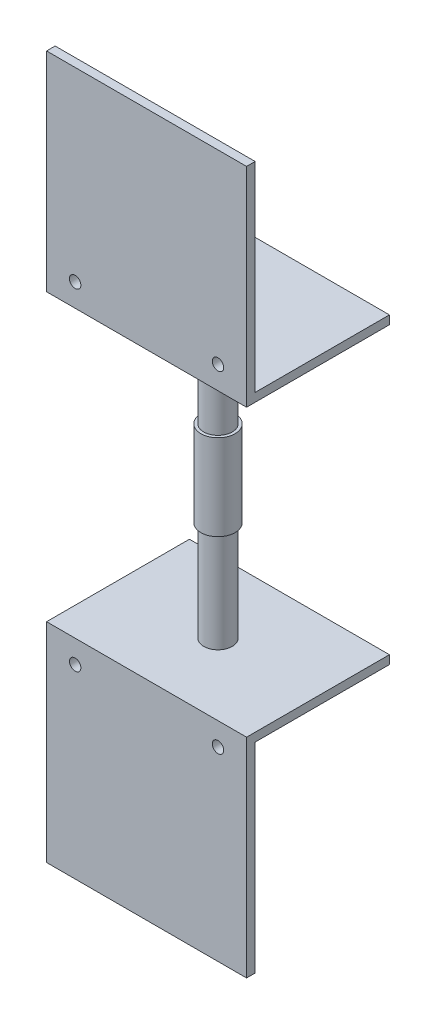
SolidWorks part; units mm, degrees
ref_plane "Front Plane" through (0, 0, 0) normal (0, 0, 1) x (1, 0, 0)
ref_plane "Top Plane" through (0, 0, 0) normal (0, 1, 0) x (1, 0, 0)
ref_plane "Right Plane" through (0, 0, 0) normal (1, 0, 0) x (0, 0, -1)
sketch "Sketch1" plane through (0, 0, 0) normal (0, 1, 0) x (1, 0, 0)
  line L1 (35, -25) -> (-35, -25)
  line L2 (35, -25) -> (35, 25)
  line L3 (35, 25) -> (-35, 25)
  line L4 (-35, -25) -> (-35, 25)
  line L5 (35, -25) -> (-35, 25) construction
  line L6 (35, 25) -> (-35, -25) construction
  point P0 (0, 0)
  dimension "D1" = 70
  dimension "D2" = 50
extrude "Boss-Extrude1" add sketch "Sketch1" along normal blind 3
sketch "Sketch2" plane through (0, 3, 0) normal (0, 1, 0) x (1, 0, 0)
  line L0 (35, -25) -> (35, 25) construction
  line L1 (-35, -25) -> (35, -25)
  line L2 (-35, -25) -> (-35, -22)
  line L3 (-35, -22) -> (35, -22)
  line L4 (35, -25) -> (35, -22)
  dimension "D1" = 3
extrude "Boss-Extrude2" add sketch "Sketch2" along normal blind 70
sketch "Sketch3" plane through (0, 0, 22) normal (0, 0, -1) x (-1, 0, 0)
  line L0 (0, 3) -> (0, 82.5604) construction
  line L1 (-35, 3) -> (35, 3) construction
  line L2 (-35, 3) -> (35, 3) construction
  circle A0 centre (25, 8) radius 2
  circle A1 centre (-25, 8) radius 2
  dimension "D1" = 4
  dimension "D4" = 4
  dimension "D2" = 25
  dimension "D3" = 5
  dimension "D5" = 25
  dimension "D6" = 5
extrude "Cut-Extrude1" cut sketch "Sketch3" against normal blind 6
sketch "Sketch4" plane through (0, 0, 0) normal (0, -1, 0) x (1, 0, 0)
  circle A0 centre (0, 0) radius 5
  dimension "D1" = 10
extrude "Boss-Extrude3" add sketch "Sketch4" along normal blind 35
sketch "Sketch5" plane through (0, -35, 0) normal (0, -1, 0) x (1, 0, 0)
  circle A0 centre (0, 0) radius 6
  dimension "D1" = 12
extrude "Boss-Extrude4" add sketch "Sketch5" along normal blind 30
sketch "Sketch6" plane through (0, -65, 0) normal (0, -1, 0) x (1, 0, 0)
  circle A0 centre (0, 0) radius 5
  dimension "D1" = 10
extrude "Boss-Extrude5" add sketch "Sketch6" along normal blind 35
sketch "Sketch7" plane through (0, -100, 0) normal (0, -1, 0) x (1, 0, 0)
  line L1 (-35, -25) -> (35, -25)
  line L2 (-35, -25) -> (-35, 25)
  line L3 (-35, 25) -> (35, 25)
  line L4 (35, -25) -> (35, 25)
  line L5 (-35, -25) -> (35, 25) construction
  line L6 (-35, 25) -> (35, -25) construction
  point P0 (0, 0)
extrude "Boss-Extrude6" add sketch "Sketch7" along normal blind 3
sketch "Sketch8" plane through (0, -103, 0) normal (0, -1, 0) x (1, 0, 0)
  line L0 (35, -25) -> (35, 25) construction
  line L1 (-35, 25) -> (35, 25)
  line L2 (-35, 25) -> (-35, 22)
  line L3 (-35, 22) -> (35, 22)
  line L4 (35, 25) -> (35, 22)
  dimension "D1" = 3
extrude "Boss-Extrude7" add sketch "Sketch8" along normal blind 70
sketch "Sketch9" plane through (0, 0, 22) normal (0, 0, -1) x (-1, 0, 0)
  line L0 (0, -103) -> (0, -158.4802) construction
  line L1 (35, -103) -> (-35, -103) construction
  line L2 (35, -103) -> (-35, -103) construction
  circle A0 centre (-25, -108) radius 2
  circle A1 centre (25, -108) radius 2
  dimension "D1" = 4
  dimension "D2" = 4
  dimension "D3" = 5
  dimension "D4" = 5
  dimension "D5" = 25
  dimension "D6" = 25
extrude "Cut-Extrude2" cut sketch "Sketch9" against normal blind 70
